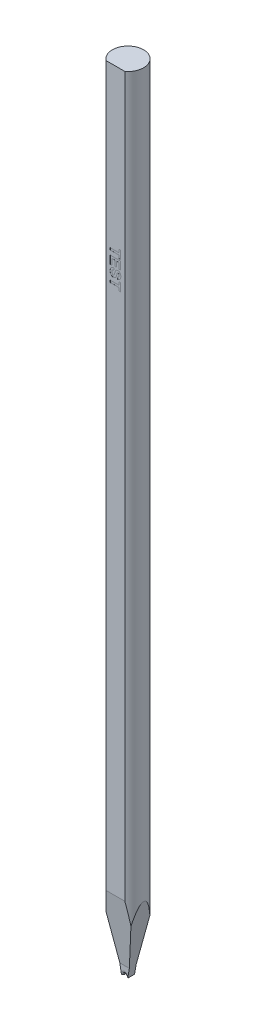
SolidWorks part; units mm, degrees
ref_plane "Ebene vorne" through (0, 0, 0) normal (0, 0, 1) x (1, 0, 0)
ref_plane "Ebene oben" through (0, 0, 0) normal (0, 1, 0) x (1, 0, 0)
ref_plane "Ebene rechts" through (0, 0, 0) normal (1, 0, 0) x (0, 0, -1)
sketch "sketch_TL_cutting" plane through (0, 0, 0) normal (0, 1, 0) x (1, 0, 0)
  circle A0 centre (0, 0) radius 1.4986
extrude "TL_cutting" add sketch "sketch_TL_cutting" along normal blind 75.9968
sketch "sketch_TDF_grinding" plane through (0, 0, 0) normal (0, 1, 0) x (1, 0, 0)
  line L0 (0, 0) -> (0, -1.2014) construction
  line L1 (-1.5086, -4.2186) -> (1.5086, -4.2186)
  line L2 (-1.5086, -4.2186) -> (-1.5086, -1.2014)
  line L3 (-1.5086, -1.2014) -> (1.5086, -1.2014)
  line L4 (1.5086, -4.2186) -> (1.5086, -1.2014)
  circle A1 centre (0, 0) radius 1.4986 construction
  point P9 (0, -4.2186)
  dimension "TD_2Offset_X" = 3.0172
  dimension "TD_2Offset_Z" = 3.0172
extrude "TDF_grinding" cut sketch "sketch_TDF_grinding" along normal through all
sketch "sketch_engraving" plane through (0, 0, 1.2014) normal (0, 0, 1) x (1, 0, 0)
  line L0 (0.8958, 75.9968) -> (-0.8958, 75.9968) construction
  line L6 (-0.8958, 0) -> (0.8958, 0) construction
  line L7 (0, 0) -> (0, 60.9968) construction
  line L8 (-0.5, 60.9968) -> (-0.5, 0) construction
  text T0 "TEST" font "Arial" height 1
  dimension "D2" = 0.5
  dimension "EngravingStart" = 15
extrude "engraving" cut sketch "sketch_engraving" against normal blind 0.005
sketch "sketch_VW_VR_grinding" plane through (0, 0, 0) normal (0, 0, 1) x (1, 0, 0)
  line L0 (-1.4936, -0.01) -> (-1.4936, 0.874)
  line L1 (1.4936, -0.01) -> (1.4936, 0.874)
  line L2 (-1.4936, 0) -> (1.4936, 0) construction
  line L3 (-1.5086, 0.879) -> (-1.4986, 0.879)
  line L4 (1.4986, 0.879) -> (1.5086, 0.879)
  line L5 (-1.5086, 0.879) -> (-1.5086, -0.01)
  line L6 (-1.5086, -0.01) -> (-1.4936, -0.01)
  line L7 (1.4936, -0.01) -> (1.5086, -0.01)
  line L8 (1.5086, -0.01) -> (1.5086, 0.879)
  line L9 (-1.4986, 0.879) -> (-1.4986, 0.874) construction
  line L10 (-1.4936, 0.874) -> (-1.4986, 0.874) construction
  line L11 (1.4936, 0.874) -> (1.4986, 0.874) construction
  line L12 (1.4986, 0.879) -> (1.4986, 0.874) construction
  arc A0 (-1.4986, 0.879) -> (-1.4936, 0.874) centre (-1.4986, 0.874) cw
  arc A2 (1.4936, 0.874) -> (1.4986, 0.879) centre (1.4986, 0.874) cw
  dimension "D2" = 0.005
  dimension "D1" = 0.01
  dimension "D4" = 3.0172
extrude "VW_VR_grinding" cut sketch "sketch_VW_VR_grinding" against normal blind 1.5086 and the other way blind 1.5086
sketch "sketch_ISA_grinding" plane through (0, 0, 0) normal (0, 0, 1) x (1, 0, 0)
  line L0 (-0.2997, 0) -> (-1.5086, 6.8559)
  line L4 (1.5086, 6.8559) -> (0.2997, 0)
  line L5 (0.2997, 0) -> (-0.2997, 0)
  line L6 (0, 0) -> (0, 30.49) construction
  line L7 (-1.5086, 6.8559) -> (-1.5086, -0.01)
  line L12 (-1.5086, -0.01) -> (1.5086, -0.01)
  line L13 (1.5086, -0.01) -> (1.5086, 6.8559)
  dimension "ISA" = 20
  dimension "TD_2Offset" = 3.0172
  dimension "Offset" = 0.01
extrude "ISA_grinding" cut sketch "sketch_ISA_grinding" against normal blind 1.5086 and the other way blind 1.5086
sketch "sketch_pre_FRX_BRX" plane through (0, 0, 0) normal (1, 0, 0) x (0, 0, -1)
  line L0 (1.4986, -0.01) -> (1.4986, 3.9152) construction
  line L1 (-1.2014, -0.01) -> (-1.2014, 0.879) construction
  line L2 (-0.3251, -0.01) -> (-0.3251, 0.879)
  line L3 (-0.3251, 0.879) -> (-1.5086, 0.879)
  line L4 (-1.5086, 0.879) -> (-1.5086, -0.01)
  line L5 (-1.5086, -0.01) -> (-0.3251, -0.01)
  line L6 (0.3251, -0.01) -> (0.3251, 0.879)
  line L7 (0.3251, 0.879) -> (1.5086, 0.879)
  line L8 (1.5086, 0.879) -> (1.5086, -0.01)
  line L9 (1.5086, -0.01) -> (0.3251, -0.01)
  dimension "D3" = 0.01
  dimension "D4" = 0.889
  dimension "D5" = 3.0172
  dimension "D6" = 0.6502
  dimension "D2" = 0.01
  dimension "D7" = 1.8237
extrude "pre_FRX_BRX" cut sketch "sketch_pre_FRX_BRX" against normal blind 1.5086 and the other way blind 1.5086
sketch "sketch_contour_V-Groove" plane through (0, 0, 0) normal (1, 0, 0) x (0, 0, -1)
  line L0 (-1.2014, 0.1905) -> (0, 0.1905)
  line L1 (0, 0.1905) -> (1.4986, 0.1905)
  line L2 (1.4986, -0.8411) -> (1.4986, 1.3178) construction
  line L3 (-1.2014, -0.9209) -> (-1.2014, 1.9363) construction
  line L4 (-1.2014, 0) -> (1.4986, 0) construction
  line L5 (0.3251, 0) -> (0.3251, 0.1905) construction
  line L6 (-0.3251, 0) -> (-0.3251, 0.1905) construction
  dimension "D1" = 0
ref_plane "front" through (0, 0, 1.2014) normal (0, 0, 1) x (1, 0, 0)
ref_plane "back" through (0, 0, -1.4986) normal (0, 0, 1) x (1, 0, 0)
sketch "sketch_section_V-Groove" plane through (0, 0, 1.2014) normal (0, 0, 1) x (1, 0, 0)
  line L0 (-1.499, -1.905) -> (-0.0499, 0.1645)
  line L2 (0.0499, 0.1645) -> (1.499, -1.905)
  line L3 (-1.499, -1.905) -> (1.499, -1.905)
  line L4 (0, -1.905) -> (0, 0.1905) construction
  line L5 (-0.1651, 0) -> (0.1651, 0) construction
  arc A0 (0.0499, 0.1645) -> (-0.0499, 0.1645) centre (0, 0.1296) ccw
  dimension "GA" = 70
sweep "V-Groove_EDM" cut profiles "sketch_section_V-Groove" path "sketch_contour_V-Groove"
fillet "FR_EDM" radius 0.2261 3 edges at (0.1075, 0.0823, 0.3251) (0, 0.1905, 0.3251) (-0.1075, 0.0823, 0.3251)
fillet "BR_EDM" radius 0.2261 3 edges at (0.1075, 0.0823, -0.3251) (0, 0.1905, -0.3251) (-0.1075, 0.0823, -0.3251)
sketch "sketch_FA_BA_grinding" plane through (0, 0, 0) normal (1, 0, 0) x (0, 0, -1)
  line L2 (2.4986, 16.3541) -> (2.4986, -0.1)
  line L3 (2.4986, -0.1) -> (0.3251, -0.1)
  line L5 (0.3251, -0.1) -> (0.3251, 0.889)
  line L6 (0.3251, 0.889) -> (2.4986, 16.3541)
  line L7 (1.4986, -0.1) -> (1.4986, 9.2387) construction
  line L8 (-1.2014, 7.1242) -> (-1.2014, -0.1) construction
  line L9 (-3.2728, 21.863) -> (-0.3251, 0.889)
  line L10 (-0.3251, 0.889) -> (-0.3251, -0.1)
  line L11 (-0.3251, -0.1) -> (-3.2728, -0.1)
  line L12 (-3.2728, -0.1) -> (-3.2728, 21.863)
  line L13 (-0.3251, 0.889) -> (0.3251, 0.889) construction
  dimension "D4" = 1
  dimension "D1" = 0.1
  dimension "FA" = 8
  dimension "BA" = 8
extrude "FA_BA_grinding" cut sketch "sketch_FA_BA_grinding" against normal blind 1.5086 and the other way blind 1.5086
sketch "sketch_groove_dimensions" plane through (0, 0, 0) normal (1, 0, 0) x (0, 0, -1)
  line L0 (-0.0991, 0.1905) -> (0.0991, 0.1905)
  line L1 (-0.3251, 0) -> (-0.3251, 0.4166) construction
  line L2 (1.4986, 0) -> (1.4986, 0.4166) construction
  line L3 (0.3251, 0) -> (0.3251, 0.4166) construction
  line L4 (-1.2014, 0) -> (-1.2014, 0.3999) construction
  arc A0 (0.0991, 0.1905) -> (0.3251, 0.4166) centre (0.0991, 0.4166) ccw
  arc A1 (-0.0991, 0.1905) -> (-0.3251, 0.4166) centre (-0.0991, 0.4166) cw
equation "\"_Offset\"=0.01mm"
equation "\"TL\"=2.992in"
equation "\"TD\"=0.1180in"
equation "\"TDF\"=0.1063in"
equation "\"BA\"=8deg"
equation "\"ISA\"=20deg"
equation "\"FA\"=8deg"
equation "\"GR\"=0.0024in"
equation "\"GA\"=70deg"
equation "\"GD\"=0.0075in"
equation "\"FL\"=0.0256in"
equation "\"F\"=0.0138in"
equation "\"FX\"=0mm"
equation "\"B\"=0.013in"
equation "\"VW\"=0in"
equation "\"cleaned_VR\"= IIF ( \"VR\" > 0 , \"VR\" , \"E\" - \"_Offset\" )"
equation "\"cleaned_VW\"= IIF ( \"VW\" > 0 , \"VW\" , \"TD\" - \"_Offset\" )"
equation "\"back_edge\"= \"TD\" / 2 - \"X\""
equation "\"side_edge_Offset\"= \"TD\" / 2 + \"_Offset\""
equation "\"TD@sketch_TL_cutting\"=\"TD\""
equation "\"TL@TL_cutting\"=\"TL\""
equation "\"TDF@sketch_TDF_grinding\"=\"TDF\""
equation "\"TD_2Offset_X@sketch_TDF_grinding\"=\"TD\"+2*\"_Offset\""
equation "\"TD_2Offset_Z@sketch_TDF_grinding\"=\"TD\"+2*\"_Offset\""
equation "\"TL_Offset\"= \"TL\" + \"_Offset\""
equation "\"ISA@sketch_ISA_grinding\"=\"ISA\""
equation "\"W@sketch_ISA_grinding\"=\"W\""
equation "\"TD_2Offset@sketch_ISA_grinding\"=\"TD\"+2*\"_Offset\""
equation "\"Offset@sketch_ISA_grinding\"=\"_Offset\""
equation "\"05TD_Offset_posZ@ISA_grinding\"=\"side_edge_Offset\""
equation "\"05TD_Offset_negZ@ISA_grinding\"=\"side_edge_Offset\""
equation "\"E\"=0.035in"
equation "\"cleaned_X\"= IIF ( \"X\" > 0 , \"X\" , \"TD\" / 2 - \"FL\" / 2 )"
equation "\"FR\"=0.0089in"
equation "\"BR\"=0.0089in"
equation "\"D1\"= \"side_edge_Offset\""
equation "\"D2\"= \"side_edge_Offset\""
equation "\"TDF@sketch_FA_BA_grinding\" = \"TDF\""
equation "\"FL@sketch_FA_BA_grinding\"=\"FL\""
equation "\"E@sketch_FA_BA_grinding\" = \"E\""
equation "\"D1@FA_BA_grinding\"=\"side_edge_Offset\""
equation "\"D2@FA_BA_grinding\"=\"side_edge_Offset\""
equation "\"10GD@sketch_section_V-Groove\" = 10 * \"GD\""
equation "\"GA@sketch_section_V-Groove\" = \"GA\""
equation "\"GD@sketch_section_V-Groove\" = \"GD\""
equation "\"B@sketch_section_V-Groove\" = \"B\""
equation "\"GD@sketch_contour_V-Groove\" = \"GD\""
equation "\"cleaned_FRX\"= IIF ( \"FRX\" > 0 , \"FRX\" , \"FR\" )"
equation "\"cleaned_BRX\"= IIF ( \"BRX\" > 0 , \"BRX\" , \"BR\" )"
equation "\"FL_groove_angle\"=0deg"
equation "\"D3@sketch_pre_FRX_BRX\" = \"_Offset\""
equation "\"D4@sketch_pre_FRX_BRX\" = \"E\""
equation "\"D5@sketch_pre_FRX_BRX\" = 2 * \"side_edge_Offset\""
equation "\"D6@sketch_pre_FRX_BRX\" = \"FL\" +  ( \"FR\" - \"cleaned_FRX\" )  +  ( \"BR\" - \"cleaned_BRX\" ) "
equation "\"TD/2@sketch_pre_FRX_BRX\" = \"TD\" / 2"
equation "\"TDF@sketch_pre_FRX_BRX\" = \"TDF\""
equation "\"D2@sketch_pre_FRX_BRX\" = \"_Offset\""
equation "\"D1@pre_FRX_BRX\" = \"side_edge_Offset\""
equation "\"D2@pre_FRX_BRX\" = \"side_edge_Offset\""
equation "\"D1@BR_EDM\"=\"BR\""
equation "\"TD/2@sketch_FA_BA_grinding\" = \"TD\" / 2"
equation "\"TD/2@sketch_contour_V-Groove\" = \"TD\" / 2"
equation "\"TDF@sketch_contour_V-Groove\" = \"TDF\""
equation "\"D1@sketch_contour_V-Groove\"=\"FL_groove_angle\""
equation "\"FL@sketch_contour_V-Groove\"=\"FL\""
equation "\"FL/2@sketch_contour_V-Groove\" = \"FL\" / 2"
equation "\"D1@FR_EDM\"=\"FR\""
equation "\"D1@sketch_VW_VR_grinding\" = \"_Offset\""
equation "\"D4@sketch_VW_VR_grinding\" = 2 * \"side_edge_Offset\""
equation "\"VR@sketch_VW_VR_grinding\" = \"cleaned_VR\""
equation "\"VW@sketch_VW_VR_grinding\"=\"cleaned_VW\""
equation "\"D1@VW_VR_grinding\" = \"side_edge_Offset\""
equation "\"D2@VW_VR_grinding\" = \"side_edge_Offset\""
equation "\"X\"=0mm"
equation "\"VR\"=0in"
equation "\"W\"=0.0236in"
equation "\"VW_radius\"= \"cleaned_VW\" / 10"
equation "\"VW_radius_cleaned\"= IIF ( \"VW\" > 0 , \"VW_radius\" , \"_Offset\" / 2 )"
equation "\"D2@sketch_VW_VR_grinding\"=\"VW_radius_cleaned\""
equation "\"FRX\"=0in"
equation "\"BRX\"=0in"
equation "\"FA@sketch_FA_BA_grinding\" = \"FA\""
equation "\"D4@sketch_FA_BA_grinding\"=\"_Offset\"*100"
equation "\"BA@sketch_FA_BA_grinding\" = \"BA\""
equation "\"D1@sketch_groove_dimensions\" = \"TD\" / 2"
equation "\"FL@sketch_groove_dimensions\" = \"FL\""
equation "\"FR@sketch_groove_dimensions\" = \"FR\""
equation "\"BR@sketch_groove_dimensions\" = \"BR\""
equation "\"FRX@sketch_groove_dimensions\" = \"cleaned_FRX\""
equation "\"BRX@sketch_groove_dimensions\" = \"cleaned_BRX\""
equation "\"GD@sketch_groove_dimensions\" = \"GD\""
equation "\"cleaned_FX\"= IIF ( \"FX\" > 0 , \"FX\" , \"TDF\" - ( \"TD\" + \"FL\" ) / 2 )"
equation "\"D7@sketch_pre_FRX_BRX\"=\"TDF\"-\"cleaned_FX\"-(\"FR\"-\"cleaned_FRX\")"
equation "\"FX@sketch_contour_V-Groove\" = \"cleaned_FX\""
equation "\"FX@sketch_FA_BA_grinding\" = \"cleaned_FX\""
equation "\"TDF@sketch_groove_dimensions\" = \"TDF\""
equation "\"FX@sketch_groove_dimensions\" = \"cleaned_FX\""
equation "\"EngravingStart\"=15mm"
equation "\"EngravingStart@sketch_engraving\" = \"EngravingStart\""
